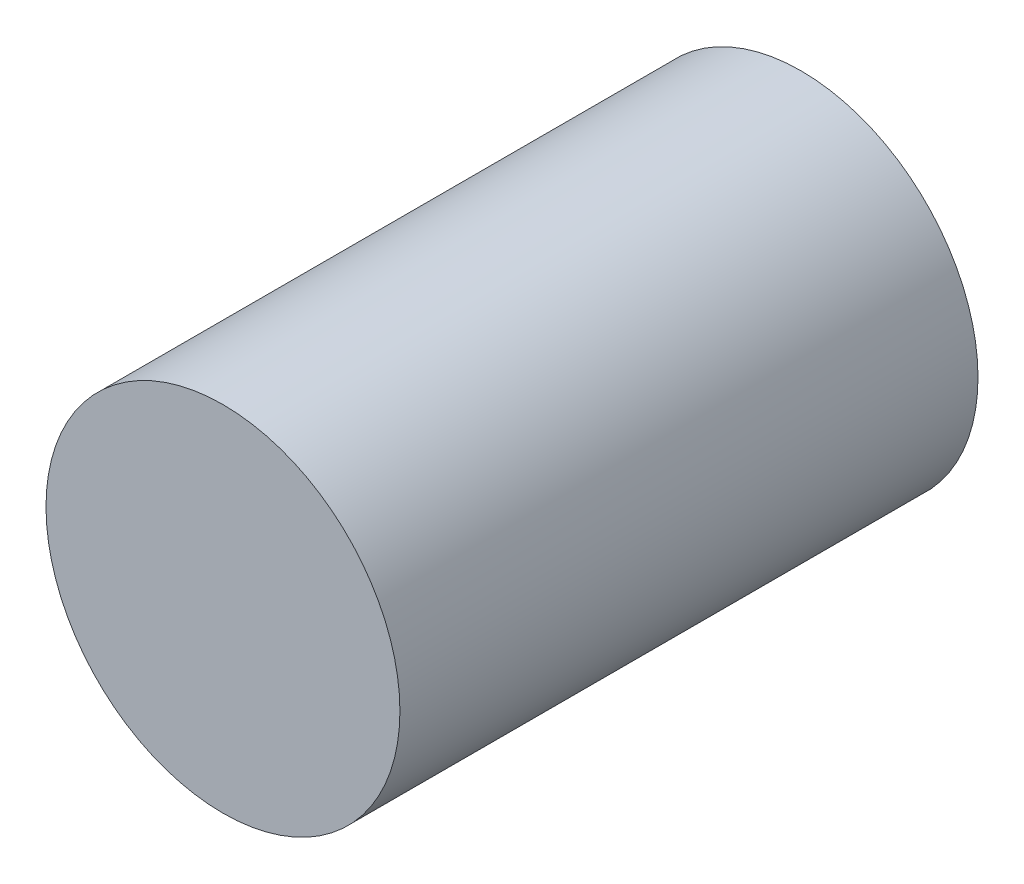
SolidWorks part; units mm, degrees
material "ABS"
ref_plane "Front Plane" through (0, 0, 0) normal (0, 0, 1) x (1, 0, 0)
ref_plane "Top Plane" through (0, 0, 0) normal (0, 1, 0) x (1, 0, 0)
ref_plane "Right Plane" through (0, 0, 0) normal (1, 0, 0) x (0, 0, -1)
sketch "Sketch1" plane through (0, 0, 0) normal (0, 0, 1) x (1, 0, 0)
  circle A0 centre (0, 0) radius 3
  dimension "D1" = 6
extrude "Boss-Extrude1" add sketch "Sketch1" along normal blind 9.8
